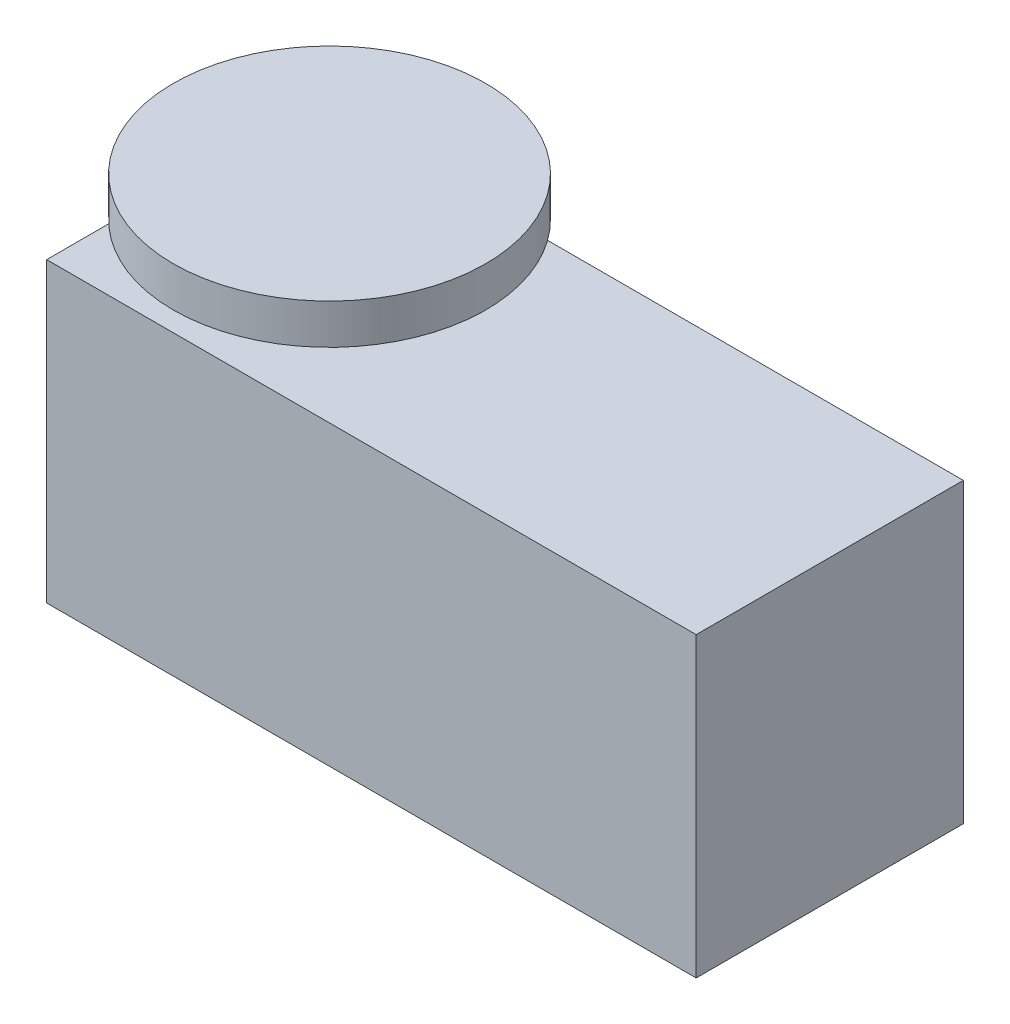
SolidWorks part; units mm, degrees
ref_plane "Front Plane" through (0, 0, 0) normal (0, 0, 1) x (1, 0, 0)
ref_plane "Top Plane" through (0, 0, 0) normal (0, 1, 0) x (1, 0, 0)
ref_plane "Right Plane" through (0, 0, 0) normal (1, 0, 0) x (0, 0, -1)
sketch "Sketch1" plane through (0, 0, 0) normal (0, 0, 1) x (1, 0, 0)
  line L1 (-24.31, -11.13) -> (24.31, -11.13)
  line L2 (-24.31, -11.13) -> (-24.31, 11.13)
  line L3 (-24.31, 11.13) -> (24.31, 11.13)
  line L4 (24.31, -11.13) -> (24.31, 11.13)
  line L5 (-24.31, -11.13) -> (24.31, 11.13) construction
  line L6 (-24.31, 11.13) -> (24.31, -11.13) construction
  point P0 (0, 0)
  dimension "D1" = 48.62
  dimension "D2" = 22.26
extrude "Boss-Extrude1" add sketch "Sketch1" along normal blind 20 contours L3 L4 L1 L2
sketch "Sketch2" plane through (0, 11.13, 0) normal (0, 1, 0) x (1, 0, 0)
  circle A0 centre (-13.7375, -9.3981) radius 1.8768
extrude "Boss-Extrude2" add sketch "Sketch2" along normal blind 2.5654
sketch "Sketch3" plane through (0, 13.6954, 0) normal (0, 1, 0) x (1, 0, 0)
  circle A0 centre (-13.7375, -9.3981) radius 11.6942
extrude "Boss-Extrude3" add sketch "Sketch3" along normal blind 3 contours A0
